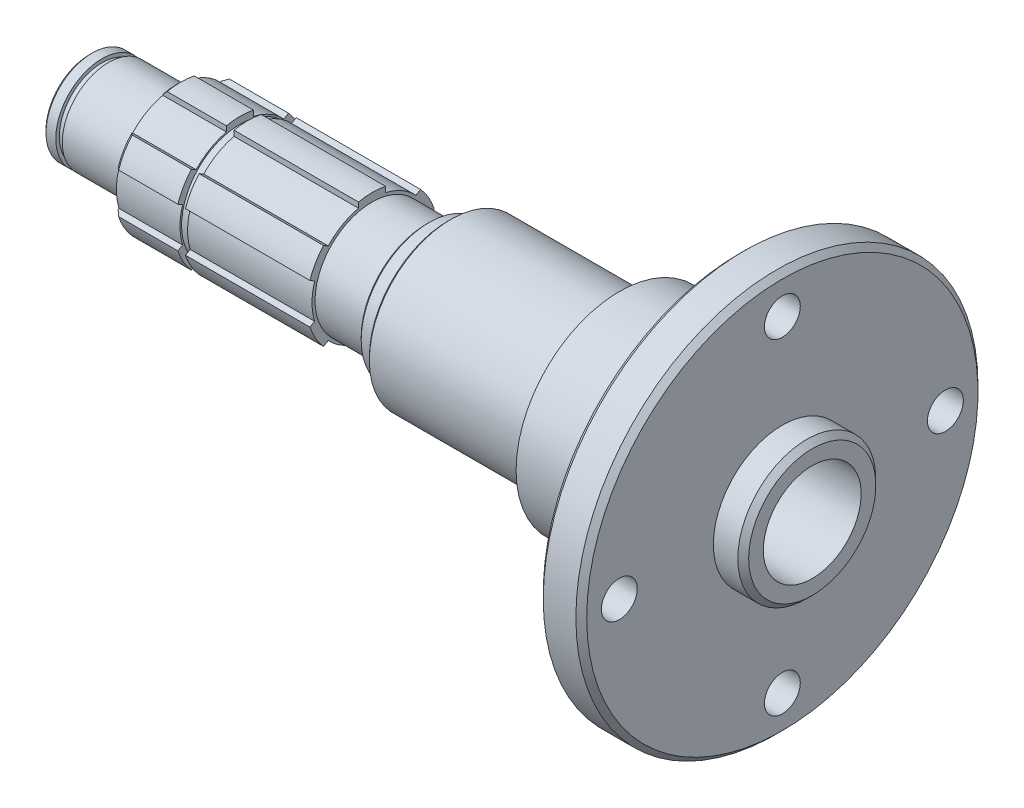
SolidWorks part; units mm, degrees
material "6063-T6"
ref_plane "Plan de face" through (0, 0, 0) normal (0, 0, 1) x (1, 0, 0)
ref_plane "Plan de dessus" through (0, 0, 0) normal (0, 1, 0) x (1, 0, 0)
ref_plane "Plan de droite" through (0, 0, 0) normal (1, 0, 0) x (0, 0, -1)
ref_axis "Axe1" through (-5.65, 0, 0) along (1, 0, 0)
sketch "Esquisse1" plane through (0, 0, 0) normal (0, 0, 1) x (1, 0, 0)
  line L0 (0, 0) -> (135, 0)
  line L1 (-44.6724, 0) -> (180.0275, 0) construction
  line L3 (0, 0) -> (0, 37.5)
  line L4 (0, 37.5) -> (135, 37.5)
  line L5 (135, 0) -> (135, 37.5)
  dimension "D1" = 135
  dimension "D2" = 75
revolve "Révolution1" add sketch "Esquisse1" angle 360 about L1
sketch "Esquisse2" plane through (0, 0, 0) normal (0, 0, 1) x (1, 0, 0)
  line L0 (0, 0) -> (0, 37.5)
  line L1 (0, 37.5) -> (135, 37.5)
  line L2 (135, 37.5) -> (135, 0)
  line L3 (135, -37.5) -> (135, 37.5) construction
  line L4 (135, 0) -> (134, 0)
  line L9 (134, 0) -> (134, 12.7)
  line L10 (134, 12.7) -> (128.5, 12.7)
  line L11 (128.5, 12.7) -> (128.5, 37)
  line L12 (128.5, 37) -> (120.5, 37)
  line L13 (120.5, 37) -> (120.5, 19)
  line L16 (120.5, 19) -> (98.5, 19)
  line L17 (98.5, 19) -> (98.5, 15)
  line L18 (98.5, 15) -> (53, 15)
  line L19 (53, 15) -> (53, 12.02)
  line L20 (53, 12.02) -> (17, 12.02)
  line L23 (17, 12.02) -> (17, 8.5)
  line L24 (17, 8.5) -> (1, 8.5)
  line L25 (1, 8.5) -> (1, 0)
  line L26 (1, 0) -> (0, 0)
  line L27 (-11.7953, 0) -> (155.2144, 0) construction
  line L28 (128.5, 30) -> (120.5, 30) construction
  line L30 (90.5, 0) -> (90.5, 62.0208) construction
  dimension "D1" = 17
  dimension "D2" = 24.04
  dimension "D3" = 30
  dimension "D4" = 74
  dimension "D5" = 25.4
  dimension "D6" = 16
  dimension "D7" = 30
  dimension "D8" = 8
  dimension "D9" = 8
  dimension "D10" = 1
  dimension "D11" = 1
  dimension "D12" = 30
  dimension "D14" = 36
  dimension "D15" = 73.5
  dimension "D16" = 38
revolve "Enlèvement de matière-Révolution1" cut sketch "Esquisse2" angle 360 about L27
hole_wizard "Dégagement M61" positions "Esquisse5" profile "Esquisse6" hole size "M6" standard "ISO" end condition through all
sketch "Esquisse5" plane through (128.5, 0, 0) normal (1, 0, 0) x (0, 0, -1)
  line L0 (0, 0) -> (0, 38.483) construction
  line L1 (0, 0) -> (17.7217, 0) construction
  point P7 (0, 30)
  dimension "D1" = 60
sketch "Esquisse6" plane through (128.5, 30, 0) normal (0, 1, 0) x (0, 0, -1)
  line L0 (0, 0) -> (0, 127.5)
  line L1 (0, 127.5) -> (3.3, 127.5)
  line L2 (3.3, 127.5) -> (3.3, 0)
  line L5 (3.3, 0) -> (0, 0)
  line L11 (0, -6.35) -> (0, 107.95) construction
  dimension "Diamètre du perçage jusqu'au prochain" = 6.6
  dimension "Profondeur du perçage jusqu'au prochain" = 127.5
pattern_circular "Répétition circulaire1" count 4 over 360 about axis through (0, 0, 0) along (1, 0, 0) of "Dégagement M61"
fillet "Congé1" radius 2 1 edges at (120.5, 0, 19)
sketch "Esquisse12" plane through (0, 0, 0) normal (0, 0, 1) x (1, 0, 0)
  line L0 (53, 12.02) -> (17, 12.02) construction
  line L1 (28.7, 12.02) -> (30.1, 12.02)
  line L2 (28.7, 12.02) -> (28.7, 10.75)
  line L3 (28.7, 10.75) -> (30.1, 10.75)
  line L4 (30.1, 12.02) -> (30.1, 10.75)
  line L5 (17, 12.02) -> (17, -12.02) construction
  line L6 (0, 0) -> (-21.8506, 0) construction
  dimension "D1" = 11.7
  dimension "D2" = 1.4
  dimension "D3" = 21.5
revolve "Enlèvement de matière-Révolution6" cut sketch "Esquisse12" angle 360 about L6
sketch "Esquisse7" plane through (17, 0, 0) normal (-1, 0, 0) x (0, 0, 1)
  line L0 (0, 0) -> (0, 17.2205) construction
  line L1 (0, 0) -> (2.5, 11.7571) construction
  line L4 (11.432, 3.7135) -> (10.5714, 3.2167)
  line L10 (2.5, 11.7571) -> (2.5, 10.7635)
  line L11 (-2.5, 11.7571) -> (-2.5, 10.7635)
  line L12 (8.932, 8.0436) -> (8.0714, 7.5468)
  line L13 (8.932, -8.0436) -> (8.0714, -7.5468)
  line L14 (11.432, -3.7135) -> (10.5714, -3.2167)
  line L15 (-2.5, -11.7571) -> (-2.5, -10.7635)
  line L16 (2.5, -11.7571) -> (2.5, -10.7635)
  line L17 (-11.432, -3.7135) -> (-10.5714, -3.2167)
  line L18 (-8.932, -8.0436) -> (-8.0714, -7.5468)
  line L19 (-8.932, 8.0436) -> (-8.0714, 7.5468)
  line L20 (-11.432, 3.7135) -> (-10.5714, 3.2167)
  arc A0 (-2.5, 11.7571) -> (2.5, 11.7571) centre (0, 0) cw
  circle A2 centre (0, 0) radius 11.05 construction
  arc A3 (8.932, 8.0436) -> (11.432, 3.7135) centre (0, 0) cw
  arc A5 (11.432, -3.7135) -> (8.932, -8.0436) centre (0, 0) cw
  arc A6 (2.5, -11.7571) -> (-2.5, -11.7571) centre (0, 0) cw
  arc A7 (-8.932, -8.0436) -> (-11.432, -3.7135) centre (0, 0) cw
  arc A8 (-11.432, 3.7135) -> (-8.932, 8.0436) centre (0, 0) cw
  arc A9 (2.5, 10.7635) -> (8.0714, 7.5468) centre (0, 0) cw
  arc A10 (10.5714, 3.2167) -> (10.5714, -3.2167) centre (0, 0) cw
  arc A11 (8.0714, -7.5468) -> (2.5, -10.7635) centre (0, 0) cw
  arc A12 (-2.5, -10.7635) -> (-8.0714, -7.5468) centre (0, 0) cw
  arc A13 (-10.5714, -3.2167) -> (-10.5714, 3.2167) centre (0, 0) cw
  arc A14 (-8.0714, 7.5468) -> (-2.5, 10.7635) centre (0, 0) cw
  circle A15 centre (0, 0) radius 12.02 construction
  circle A16 centre (0, 0) radius 13.3453
  point P29 (0, 0)
  point P32 (0, 0)
  point P43 (0, 0)
  dimension "D1" = 22.1
  dimension "D2" = 2.5
  dimension "D4" = 6
  dimension "D5" = 6
extrude "Enlèv. mat.-Extru.1" cut sketch "Esquisse7" against normal up to surface (36 mm away) up to face at (53, 0, 12.02)
sketch "Esquisse8" plane through (0, 0, 0) normal (0, 0, 1) x (1, 0, 0)
  line L0 (3.3, 8.5) -> (3.3, 7.85)
  line L1 (17, 8.5) -> (1, 8.5) construction
  line L2 (3.3, 7.85) -> (4.5, 7.85)
  line L3 (4.5, 7.85) -> (4.5, 8.5)
  line L4 (3.3, 8.5) -> (4.5, 8.5)
  line L5 (17, 12.02) -> (17, -12.02) construction
  line L6 (0, 0) -> (-9.553, 0) construction
  line L7 (-5.65, 0) -> (140.65, 0) construction
  dimension "D1" = 12.5
  dimension "D2" = 15.7
  dimension "D3" = 1.2
revolve "Enlèvement de matière-Révolution3" cut sketch "Esquisse8" angle 360 about axis through (-5.65, 0, 0) along (1, 0, 0)
chamfer "Chanfrein1" distance 0.8 angle 45 6 edges at (17, -6.01, -10.4096) (17, 6.01, -10.4096) (17, -12.02, 0) (17, -6.01, 10.4096) (17, 6.01, 10.4096) (17, 12.02, 0)
sketch "Esquisse9" plane through (0, 0, 0) normal (0, 0, 1) x (1, 0, 0)
  line L0 (-5.65, 0) -> (140.65, 0) construction
  line L1 (53, 15) -> (67, 15)
  line L2 (53, 15) -> (53, 10.5)
  line L3 (53, 10.5) -> (63, 10.5)
  line L4 (67, 15) -> (67, 12.5)
  line L5 (63, 10.5) -> (63, 12.5)
  line L6 (63, 12.5) -> (67, 12.5)
  line L7 (75.4801, 0) -> (35.7046, 0) construction
  dimension "D1" = 21
  dimension "D2" = 14
  dimension "D3" = 25
  dimension "D4" = 4
revolve "Enlèvement de matière-Révolution4" cut sketch "Esquisse9" angle 360 about axis through (-5.65, 0, 0) along (1, 0, 0)
chamfer "Chanfrein2" distance 0.5 angle 45 1 edges at (67, 0, 15)
fillet "Congé2" radius 1 1 edges at (63, 0, 10.5)
chamfer "Chanfrein3" distance 0.5 angle 45 1 edges at (1, 0, 8.5)
chamfer "Chanfrein4" distance 1 angle 45 2 edges at (128.5, 0, 37) (120.5, 0, 37)
chamfer "Chanfrein5" distance 1 angle 45 1 edges at (134, 0, 12.7)
chamfer "Chanfrein6" distance 0.5 angle 45 1 edges at (63, 0, 12.5)
sketch "Esquisse13" plane through (0, 0, 0) normal (0, 0, 1) x (1, 0, 0)
  line L0 (134, -11.7) -> (134, 11.7) construction
  line L1 (134, 9) -> (74.1962, 9)
  line L4 (74.1962, 9) -> (69, 0)
  line L5 (0, 0) -> (-33.14, 0) construction
  line L6 (-5.65, 0) -> (140.65, 0) construction
  line L7 (69, 0) -> (134, 0)
  line L8 (134, 0) -> (134, 9)
  dimension "D1" = 18
  dimension "D2" = 60
  dimension "D3" = 65
revolve "Enlèvement de matière-Révolution7" cut sketch "Esquisse13" angle 360 about axis through (-5.65, 0, 0) along (1, 0, 0)
